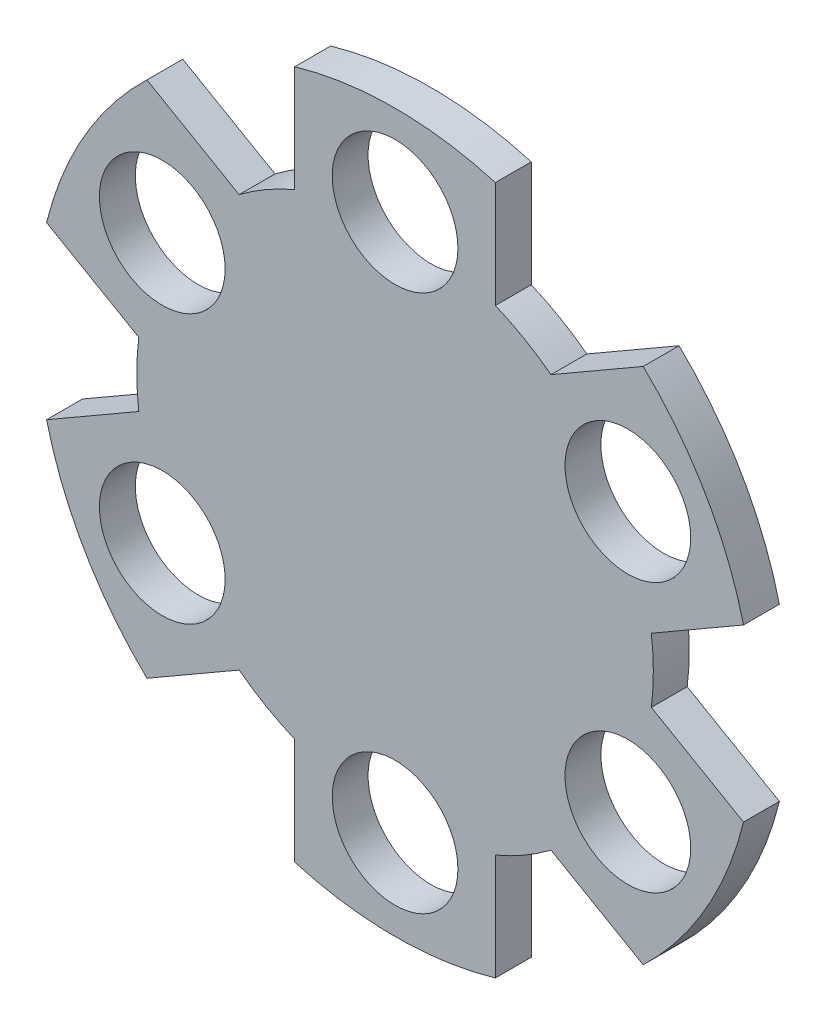
SolidWorks part; units mm, degrees
ref_plane "Front Plane" through (0, 0, 0) normal (0, 0, 1) x (1, 0, 0)
ref_plane "Top Plane" through (0, 0, 0) normal (0, 1, 0) x (1, 0, 0)
ref_plane "Right Plane" through (0, 0, 0) normal (1, 0, 0) x (0, 0, -1)
sketch "Sketch1" plane through (0, 0, 0) normal (0, 0, 1) x (1, 0, 0)
  line L0 (0, 0) -> (61.8183, 0) construction
  line L1 (-15.875, 15.875) -> (15.875, 15.875) construction
  line L2 (-15.875, 15.875) -> (-15.875, -15.875) construction
  line L3 (-15.875, -15.875) -> (15.875, -15.875) construction
  line L4 (15.875, 15.875) -> (15.875, -15.875) construction
  line L5 (0, 0) -> (0, 78.2171) construction
  circle A0 centre (0, 0) radius 31.75
  circle A1 centre (0, 23.7897) radius 5.5626
  circle A2 centre (20.6025, 11.8949) radius 5.5626
  circle A3 centre (20.6025, -11.8949) radius 5.5626
  circle A4 centre (0, -23.7897) radius 5.5626
  circle A5 centre (-20.6025, -11.8949) radius 5.5626
  circle A6 centre (-20.6025, 11.8949) radius 5.5626
  circle A7 centre (0, 0) radius 23.7897 construction
  dimension "D1" = 31.75
  dimension "D5" = 11.1252
  dimension "D6" = 63.5
  dimension "D2" = 31.75
  dimension "D3" = 15.875
  dimension "D4" = 15.875
extrude "Extrude1" add sketch "Sketch1" along normal blind 3.175
sketch "Sketch2" plane through (0, 0, 0) normal (0, 0, -1) x (-1, 0, 0)
  line L0 (0, 0) -> (0, 33.6605) construction
  line L1 (0, 0) -> (39.8265, 0) construction
  line L2 (8.8788, 21.0617) -> (8.8788, 30.4833)
  line L6 (-8.8788, 30.4833) -> (-8.8788, 21.0617)
  line L8 (22.6794, 2.8416) -> (30.8387, 7.5524)
  line L10 (13.8006, 18.2201) -> (21.9599, 22.9309)
  line L12 (13.8006, -18.2201) -> (21.9599, -22.9309)
  line L14 (22.6794, -2.8416) -> (30.8387, -7.5524)
  line L16 (-8.8788, -21.0617) -> (-8.8788, -30.4833)
  line L17 (8.8788, -21.0617) -> (8.8788, -30.4833)
  line L18 (-22.6794, -2.8416) -> (-30.8387, -7.5524)
  line L19 (-13.8006, -18.2201) -> (-21.9599, -22.9309)
  line L20 (-13.8006, 18.2201) -> (-21.9599, 22.9309)
  line L21 (-22.6794, 2.8416) -> (-30.8387, 7.5524)
  line L38 (-8.8788, 21.0617) -> (-8.8788, 30.4833) [skipped]
  circle A0 centre (0, 0) radius 22.8567 construction
  circle A1 centre (0, 0) radius 31.75 construction
  arc A3 (8.8788, 21.0617) -> (13.8006, 18.2201) centre (0, 0) cw
  arc A4 (8.8788, 30.4833) -> (21.9599, 22.9309) centre (0, 0) cw
  arc A5 (22.6794, 2.8416) -> (22.6794, -2.8416) centre (0, 0) cw
  arc A6 (30.8387, 7.5524) -> (30.8387, -7.5524) centre (0, 0) cw
  arc A7 (13.8006, -18.2201) -> (8.8788, -21.0617) centre (0, 0) cw
  arc A8 (21.9599, -22.9309) -> (8.8788, -30.4833) centre (0, 0) cw
  arc A9 (-8.8788, -21.0617) -> (-13.8006, -18.2201) centre (0, 0) cw
  arc A10 (-8.8788, -30.4833) -> (-21.9599, -22.9309) centre (0, 0) cw
  arc A11 (-22.6794, -2.8416) -> (-22.6794, 2.8416) centre (0, 0) cw
  arc A12 (-30.8387, -7.5524) -> (-30.8387, 7.5524) centre (0, 0) cw
  arc A13 (-13.8006, 18.2201) -> (-8.8788, 21.0617) centre (0, 0) cw
  arc A14 (-21.9599, 22.9309) -> (-8.8788, 30.4833) centre (0, 0) cw
extrude "Cut-Extrude1" cut sketch "Sketch2" against normal through all
equation "\"D3@Sketch1\" = \"D1@Sketch1\" / 2"
equation "\"D4@Sketch1\"=\"D2@Sketch1\" / 2"
